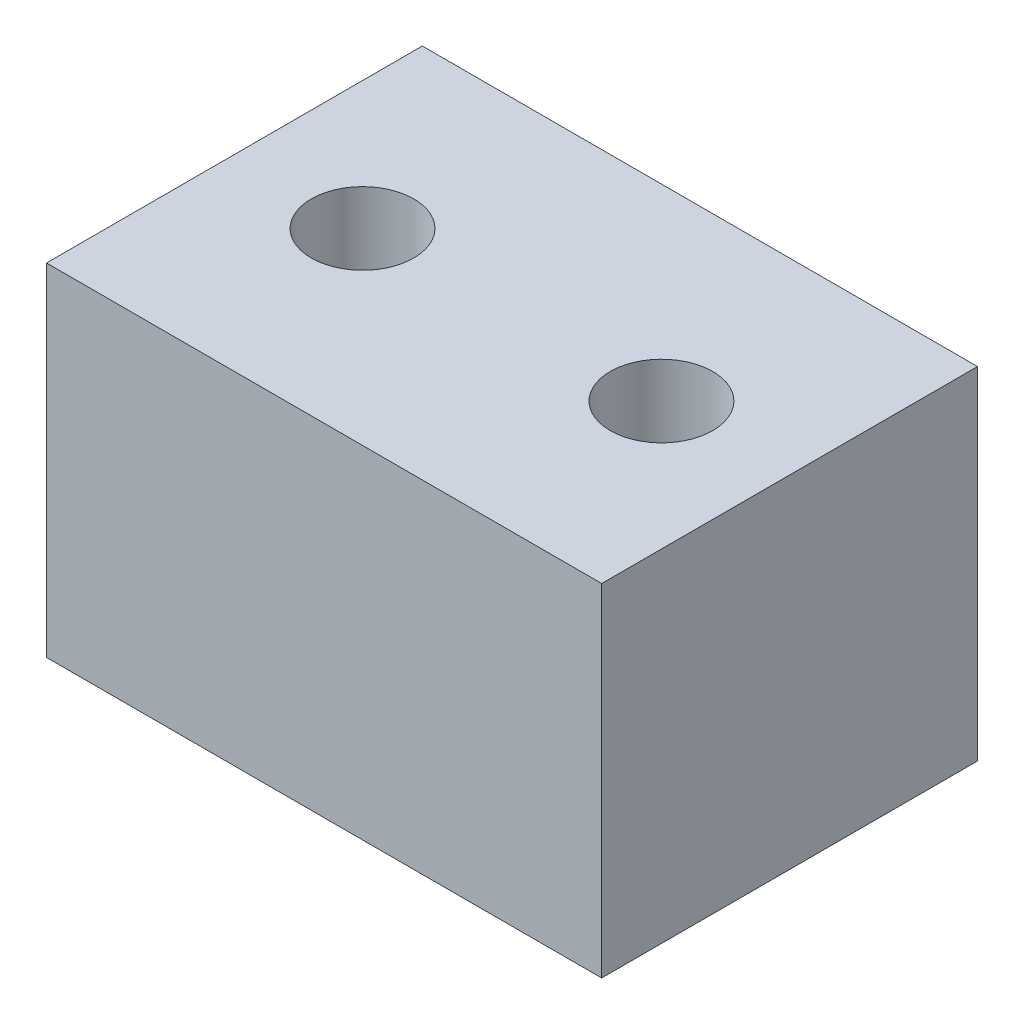
SolidWorks part; units mm, degrees
ref_plane "Front" through (0, 0, 0) normal (0, 0, 1) x (1, 0, 0)
ref_plane "Top" through (0, 0, 0) normal (0, 1, 0) x (1, 0, 0)
ref_plane "Right" through (0, 0, 0) normal (1, 0, 0) x (0, 0, -1)
sketch "Sketch1" plane through (0, 0, 0) normal (0, 1, 0) x (1, 0, 0)
  line L0 (-52.291, 28.628) -> (-52.291, -15.372)
  line L1 (-52.291, -15.372) -> (12.709, -15.372)
  line L2 (12.709, -15.372) -> (12.709, 28.628)
  line L3 (12.709, 28.628) -> (-52.291, 28.628)
  line L4 (12.709, 28.628) -> (12.709, 6.628)
  line L6 (-52.291, 28.628) -> (-52.291, 6.628)
  circle A1 centre (-37.291, 6.628) radius 6
  circle A2 centre (-2.291, 6.628) radius 6
  point P10 (0, 0)
  point P11 (0, 0)
  point P12 (0, 0)
  point P13 (0, 0)
extrude "Boss-Extrude1" add sketch "Sketch1" along normal blind 40 contours L2 L3 L0 L1 A2 A1
